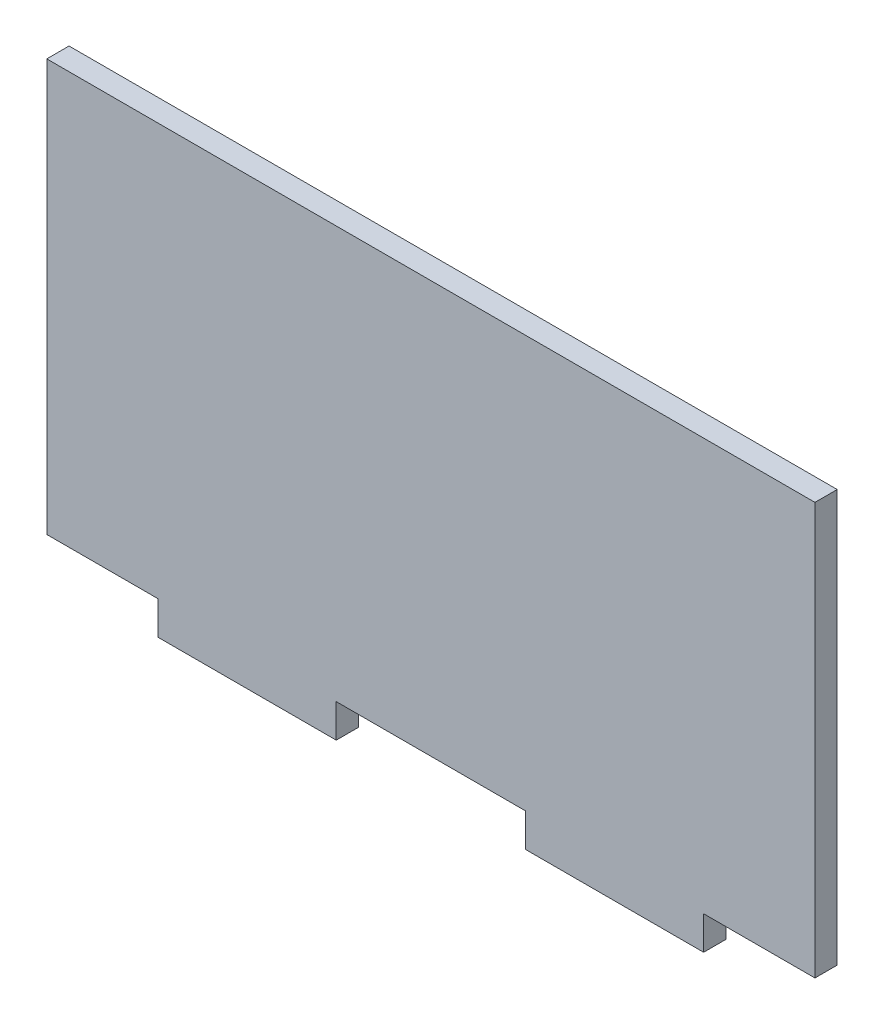
SolidWorks part; units mm, degrees
ref_plane "Front Plane" through (0, 0, 0) normal (0, 0, 1) x (1, 0, 0)
ref_plane "Top Plane" through (0, 0, 0) normal (0, 1, 0) x (1, 0, 0)
ref_plane "Right Plane" through (0, 0, 0) normal (1, 0, 0) x (0, 0, -1)
sketch "Sketch1" plane through (0, 0, 0) normal (0, 0, 1) x (1, 0, 0)
  line L4 (0, -32.7347) -> (0, 32.7347) construction
  line L5 (-34.5, -20) -> (34.5, -20)
  line L6 (-34.5, -20) -> (-34.5, 20)
  line L7 (-34.5, 20) -> (34.5, 20)
  line L8 (34.5, -20) -> (34.5, 20)
  line L9 (-34.5, -20) -> (34.5, 20) construction
  line L10 (-34.5, 20) -> (34.5, -20) construction
  line L11 (-8.5, -20) -> (-34.5, -20)
  line L12 (-8.5, -20) -> (-8.5, -17)
  line L13 (-8.5, -17) -> (-34.5, -17)
  line L14 (-34.5, -20) -> (-34.5, -17)
  line L15 (8.5, -20) -> (8.5, -17)
  line L16 (8.5, -17) -> (34.5, -17)
  line L17 (-8.5, -17) -> (8.5, -17)
  line L18 (24.5, -20) -> (24.5, -17)
  line L19 (-24.5, -20) -> (-24.5, -17)
  point P0 (0, 0)
  point P9 (0, -20)
  point P13 (0, 0)
  dimension "D1" = 40
  dimension "D2" = 69
  dimension "D3" = 8.5
  dimension "D4" = 3
  dimension "D5" = 24.5
extrude "Boss-Extrude1" add sketch "Sketch1" along normal blind 2 contours L13 L17 L16 L8 L7 L6 | L16 L15 L5 L8 | L19 L11 L12 L13
